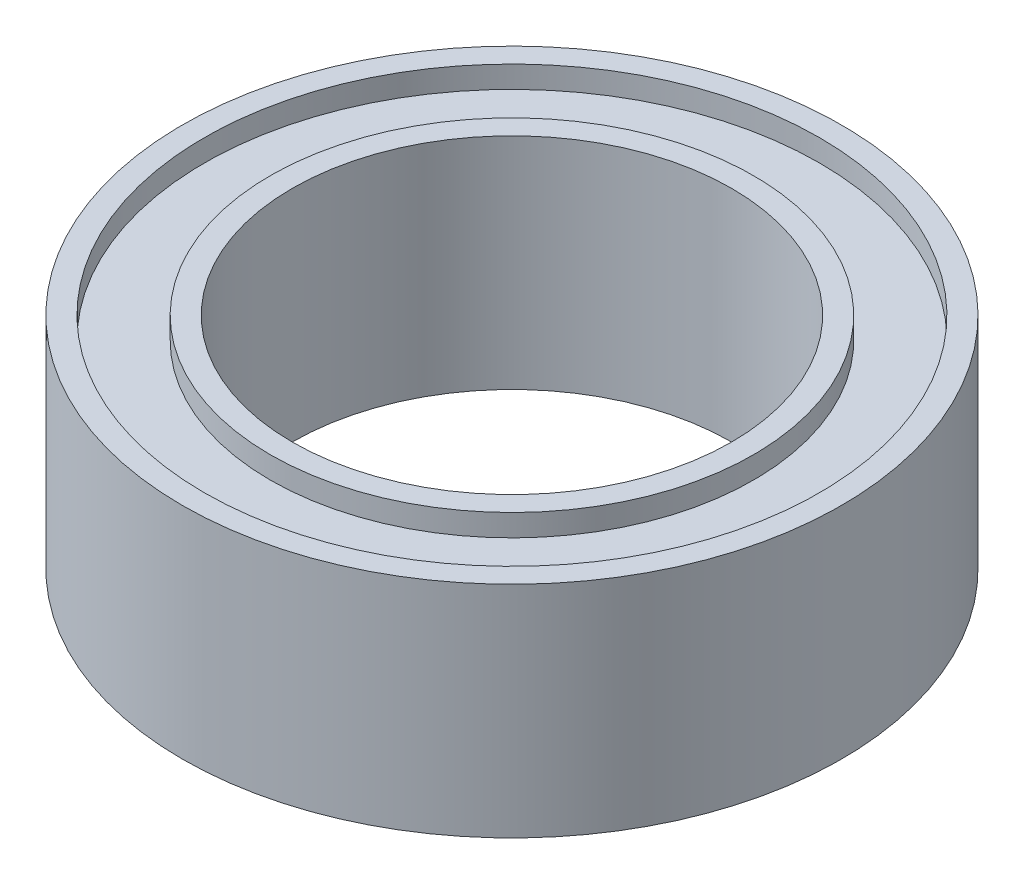
SolidWorks part; units mm, degrees
ref_plane "Front Plane" through (0, 0, 0) normal (0, 0, 1) x (1, 0, 0)
ref_plane "Top Plane" through (0, 0, 0) normal (0, 1, 0) x (1, 0, 0)
ref_plane "Right Plane" through (0, 0, 0) normal (1, 0, 0) x (0, 0, -1)
sketch "Sketch1" plane through (0, 0, 0) normal (0, 1, 0) x (1, 0, 0)
  circle A0 centre (0, 0) radius 5
  circle A1 centre (0, 0) radius 7.5
  dimension "D1" = 15
  dimension "D2" = 10
extrude "Boss-Extrude1" add sketch "Sketch1" along normal blind 5
sketch "Sketch2" plane through (0, 5, 0) normal (0, 1, 0) x (1, 0, 0)
  circle A5 centre (0, 0) radius 7
  circle A6 centre (0, 0) radius 7
  circle A8 centre (0, 0) radius 5.5
  circle A9 centre (0, 0) radius 5.5
  dimension "D1" = 0.5
  dimension "D2" = 0.5
extrude "Cut-Extrude1" cut sketch "Sketch2" against normal blind 0.5
ref_plane "Plane1" through (0, 2.5, 0) normal (0, -1, 0) x (-1, 0, 0)
mirror "Mirror1" about plane through (0, 2.5, 0) normal (0, -1, 0) of "Cut-Extrude1"
